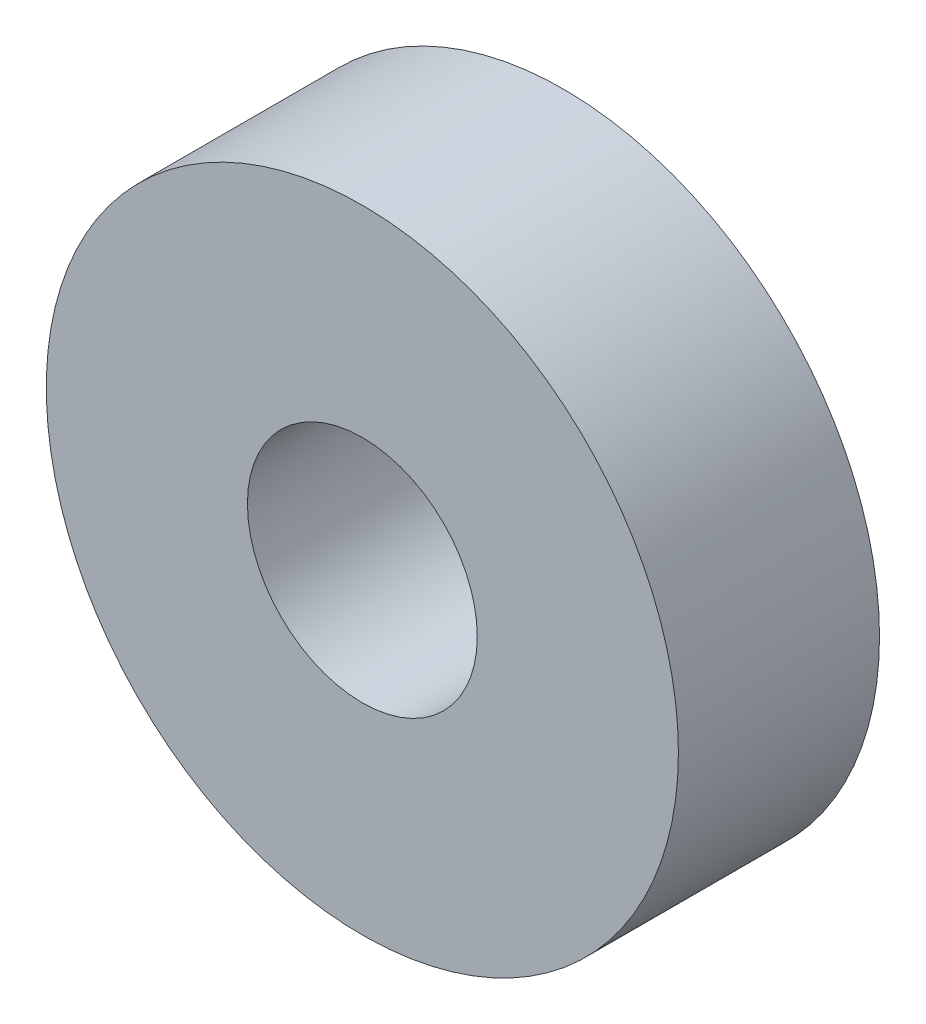
SolidWorks part; units mm, degrees
ref_plane "Plan de face" through (0, 0, 0) normal (0, 0, 1) x (1, 0, 0)
ref_plane "Plan de dessus" through (0, 0, 0) normal (0, 1, 0) x (1, 0, 0)
ref_plane "Plan de droite" through (0, 0, 0) normal (1, 0, 0) x (0, 0, -1)
sketch "Esquisse1" plane through (0, 0, 0) normal (0, 0, 1) x (1, 0, 0)
  circle A0 centre (0, 0) radius 11
  circle A1 centre (0, 0) radius 4
  dimension "D1" = 22
  dimension "D2" = 8
extrude "Boss.-Extru.1" add sketch "Esquisse1" along normal blind 7
